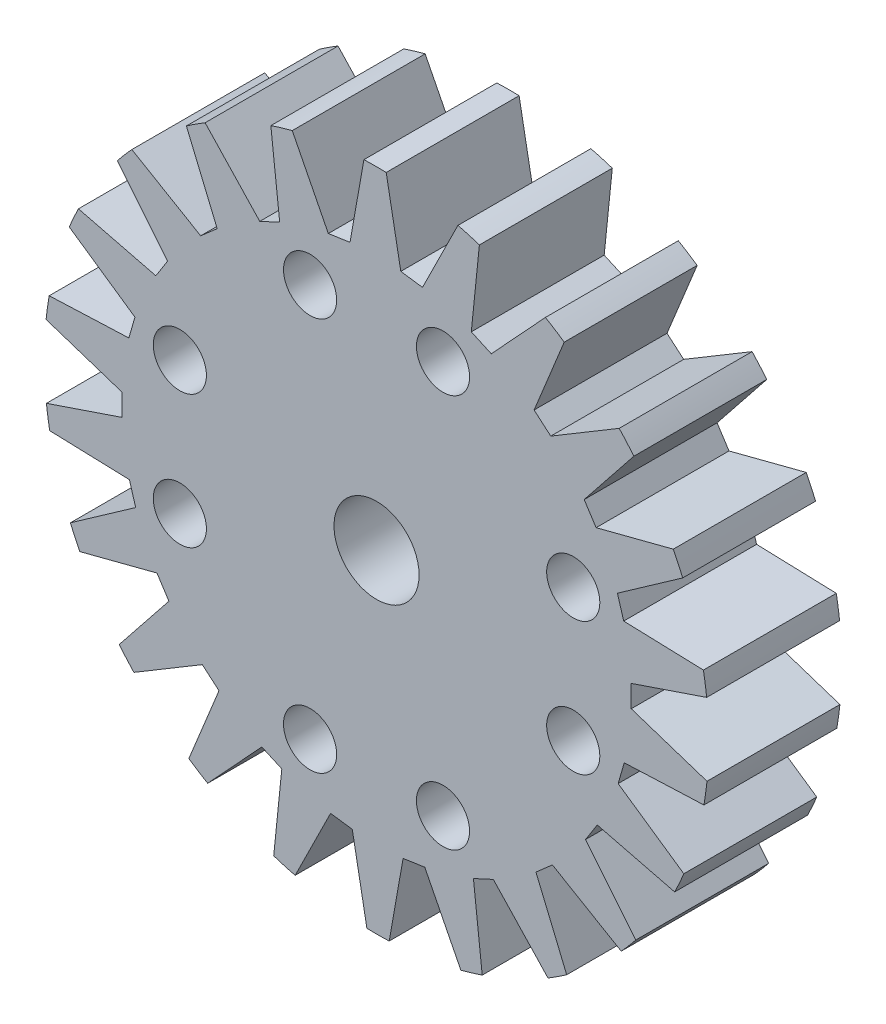
SolidWorks part; units mm, degrees
other "Markup1"
sketch "Sketch3" plane through (-11.5, 11.4999, 3) normal (-0.0441, 0.0247, 0.9987) x (0.9973, -0.0583, 0.0455)
ref_plane "Front Plane" through (0, 0, 0) normal (0, 0, 1) x (1, 0, 0)
ref_plane "Top Plane" through (0, 0, 0) normal (0, 1, 0) x (1, 0, 0)
ref_plane "Right Plane" through (0, 0, 0) normal (1, 0, 0) x (0, 0, -1)
sketch "Sketch1" plane through (0, 0, 0) normal (0, 0, 1) x (1, 0, 0)
  line L2 (-2.5, 7.4) -> (2.5, 7.4) construction
  line L3 (-2.5, -7.4) -> (2.5, -7.4) construction
  line L4 (-7.4, -2.5) -> (-7.4, 2.5) construction
  line L5 (7.4, -2.5) -> (7.4, 2.5) construction
  circle A0 centre (0, 0) radius 12.5
  circle A1 centre (0, 0) radius 10.5 construction
  circle A2 centre (0, 0) radius 1.6
  circle A3 centre (-2.5, 7.4) radius 1
  circle A5 centre (2.5, 7.4) radius 1
  circle A6 centre (2.5, -7.4) radius 1
  circle A8 centre (-2.5, -7.4) radius 1
  circle A9 centre (7.4, -2.5) radius 1
  circle A11 centre (7.4, 2.5) radius 1
  circle A12 centre (-7.4, 2.5) radius 1
  circle A14 centre (-7.4, -2.5) radius 1
  dimension "D1" = 25
  dimension "D2" = 21
  dimension "3,2" = 3.2
  dimension "D4" = 2
  dimension "D6" = 2
  dimension "D10" = 2
  dimension "D12" = 2
extrude "Boss-Extrude1" add sketch "Sketch1" along normal blind 5
sketch "Sketch2" plane through (0, 0, 5) normal (0, 0, 1) x (1, 0, 0)
  line L1 (-9.205, 8.4568) -> (-6.6167, 6.9401)
  line L2 (-6.6167, 6.9401) -> (-5.9956, 7.4831)
  line L3 (-5.9956, 7.4831) -> (-7.1537, 10.2506)
  line L4 (-6.6167, 6.9401) -> (-8.9503, 4.8994) construction
  line L5 (-8.9503, 4.8994) -> (-10.1083, 7.6669) construction
  line L6 (-10.1083, 7.6669) -> (-9.205, 8.4568) construction
  line L7 (-7.1537, 10.2506) -> (-7.4561, 10.5965)
  line L9 (-7.4561, 10.5965) -> (-9.5074, 8.8027)
  line L10 (-9.205, 8.4568) -> (-9.5074, 8.8027)
  circle A0 centre (0, 0) radius 11.0385 construction
  circle A1 centre (0, 0) radius 12.5 construction
  point P11 (-6.5746, 8.8669)
  point P12 (-7.9108, 7.6985)
  dimension "D1" = 2.725
  dimension "D2" = 0.825
  dimension "D4" = 3
  dimension "D5" = 3.1
  dimension "D6" = 1.2
extrude "Cut-Extrude1" cut sketch "Sketch2" against normal through all
pattern_circular "CirPattern1" count 22 over 360 about axis through (0, 0, 0) along (0, 0, 1) of "Cut-Extrude1"
